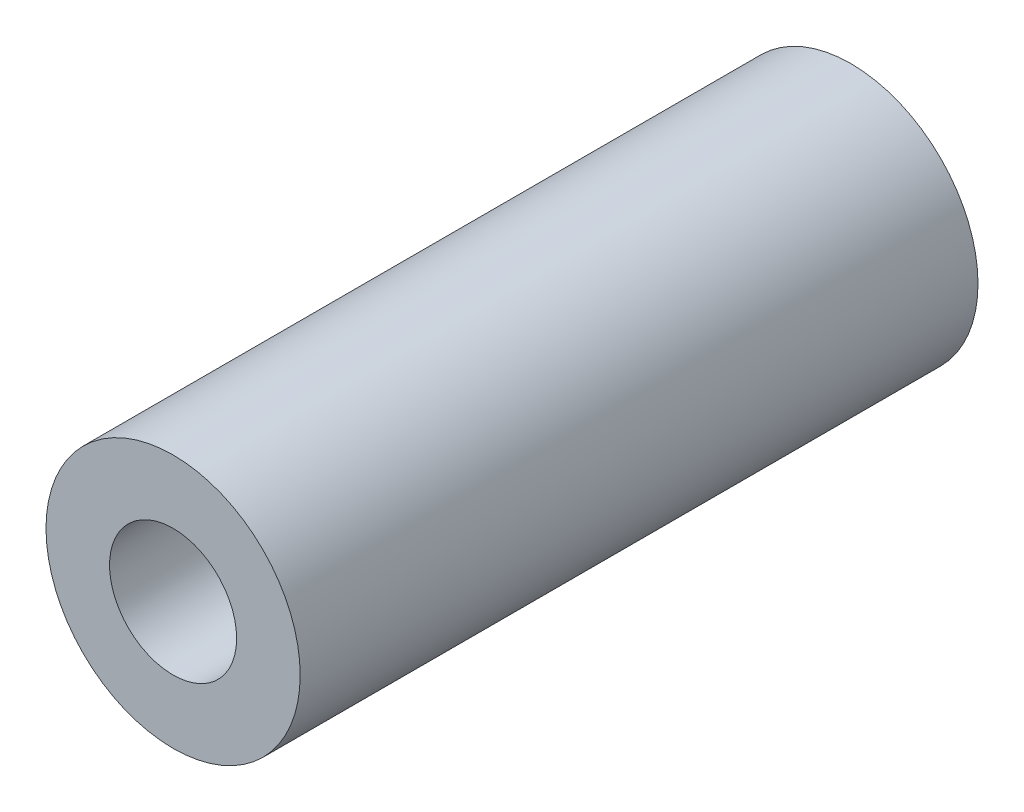
SolidWorks part; units mm, degrees
ref_plane "Plano frontal" through (0, 0, 0) normal (0, 0, 1) x (1, 0, 0)
ref_plane "Plano superior" through (0, 0, 0) normal (0, 1, 0) x (1, 0, 0)
ref_plane "Plano direito" through (0, 0, 0) normal (1, 0, 0) x (0, 0, -1)
sketch "Sketch1" plane through (0, 0, 0) normal (0, 0, 1) x (1, 0, 0)
  circle A0 centre (0, 0) radius 1.5
  circle A1 centre (0, 0) radius 3
extrude "Boss-Extrude1" add sketch "Sketch1" along normal blind 16
